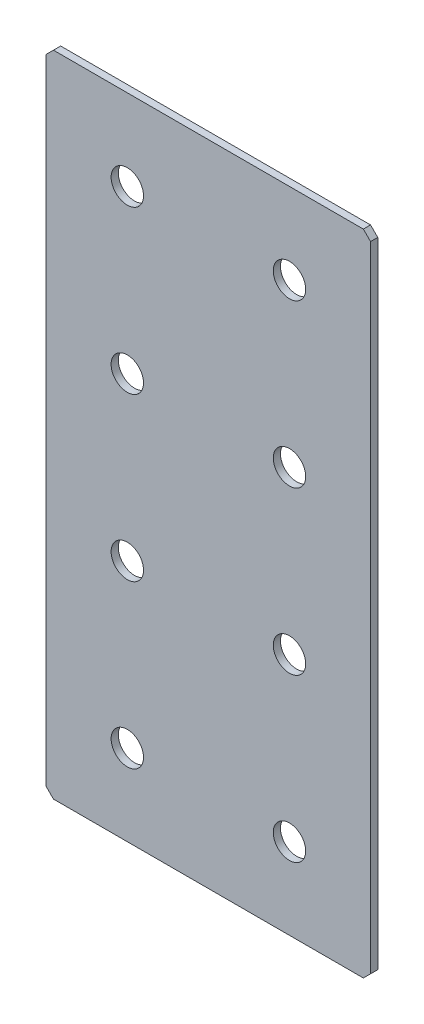
SolidWorks part; units mm, degrees
material "Простая углеродистая сталь"
ref_plane "Спереди(Плоскость XY)" through (0, 0, 0) normal (0, 0, 1) x (1, 0, 0)
ref_plane "Сверху(Плоскость XZ)" through (0, 0, 0) normal (0, 1, 0) x (1, 0, 0)
ref_plane "Справа(Плоскость ZY)" through (0, 0, 0) normal (1, 0, 0) x (0, 0, -1)
sketch "Эскиз1" plane through (0, 0, 0) normal (0, 0, 1) x (1, 0, 0)
  line L1 (-45, -90) -> (45, -90)
  line L2 (-45, -90) -> (-45, 90)
  line L3 (-45, 90) -> (45, 90)
  line L4 (45, -90) -> (45, 90)
  line L5 (-45, -90) -> (45, 90) construction
  line L6 (-45, 90) -> (45, -90) construction
  point P0 (0, 0)
  dimension "D1" = 90
  dimension "D2" = 180
extrude "Бобышка-Вытянуть1" add sketch "Эскиз1" along normal blind 2
chamfer "Фаска1" distance 2 angle 45 4 edges at (-45, -90, 1) (45, -90, 1) (-45, 90, 1) (45, 90, 1)
hole_wizard "Отверстие с зазором M81" positions "Эскиз2" profile "Эскиз3" hole size "M8" standard "DIN" end condition through all
sketch "Эскиз2" plane through (0, 0, 2) normal (0, 0, 1) x (1, 0, 0)
  line L2 (-22.5, 22.5) -> (22.5, 22.5) construction
  line L3 (-22.5, 22.5) -> (-22.5, 67.5) construction
  line L4 (-22.5, 67.5) -> (22.5, 67.5) construction
  line L5 (22.5, 22.5) -> (22.5, 67.5) construction
  line L7 (-22.5, -22.5) -> (22.5, -22.5) construction
  line L8 (-22.5, -22.5) -> (-22.5, -67.5) construction
  line L9 (-22.5, -67.5) -> (22.5, -67.5) construction
  line L10 (22.5, -22.5) -> (22.5, -67.5) construction
  line L11 (0, 22.5) -> (0, -22.5) construction
  point P0 (-22.5, 22.5)
  point P2 (22.5, 22.5)
  point P8 (-22.5, -22.5)
  point P10 (22.5, -22.5)
  point P22 (-22.5, 67.5)
  point P24 (22.5, 67.5)
  point P93 (22.5, -67.5)
  point P170 (-22.5, -67.5)
  dimension "D1" = 45
sketch "Эскиз3" plane through (-22.5, 22.5, 2) normal (1, 0, 0) x (0, -1, 0)
  line L0 (0, 0) -> (0, 2)
  line L1 (0, 2) -> (4.5, 2)
  line L2 (4.5, 2) -> (4.5, 0)
  line L5 (4.5, 0) -> (0, 0)
  line L11 (0, -6.35) -> (0, 107.95) construction
  dimension "Диаметр сквозного отверстия" = 9
  dimension "Глубина сквозного отверстия" = 2
